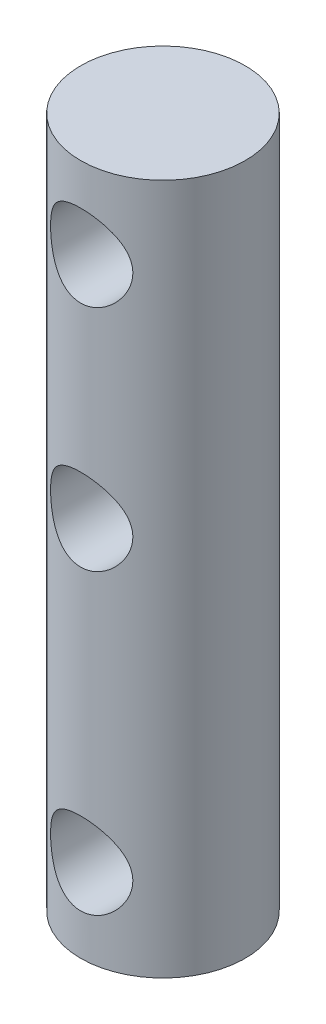
SolidWorks part; units mm, degrees
material "Plain Carbon Steel"
ref_plane "Front Plane" through (0, 0, 0) normal (0, 0, 1) x (1, 0, 0)
ref_plane "Top Plane" through (0, 0, 0) normal (0, 1, 0) x (1, 0, 0)
ref_plane "Right Plane" through (0, 0, 0) normal (1, 0, 0) x (0, 0, -1)
sketch "Sketch1" plane through (0, 0, 0) normal (0, 1, 0) x (1, 0, 0)
  circle A0 centre (0, 0) radius 2.5
  dimension "D1" = 5
extrude "Boss-Extrude1" add sketch "Sketch1" along normal blind 21
sketch "Sketch2" plane through (0, 0, 0) normal (0, 0, 1) x (1, 0, 0)
  line L0 (-2.5, 0) -> (2.5, 0) construction
  line L1 (2.5, 21) -> (-2.5, 21) construction
  circle A0 centre (0, 18.5) radius 1.25
  circle A1 centre (0, 2.5) radius 1.25
  circle A2 centre (0, 11.55) radius 1.25
  dimension "D1" = 2.5
  dimension "D4" = 11.55
  dimension "D2" = 2.5
  dimension "D3" = 2.5
extrude "Cut-Extrude1" cut sketch "Sketch2" against normal through all both and the other way through all
